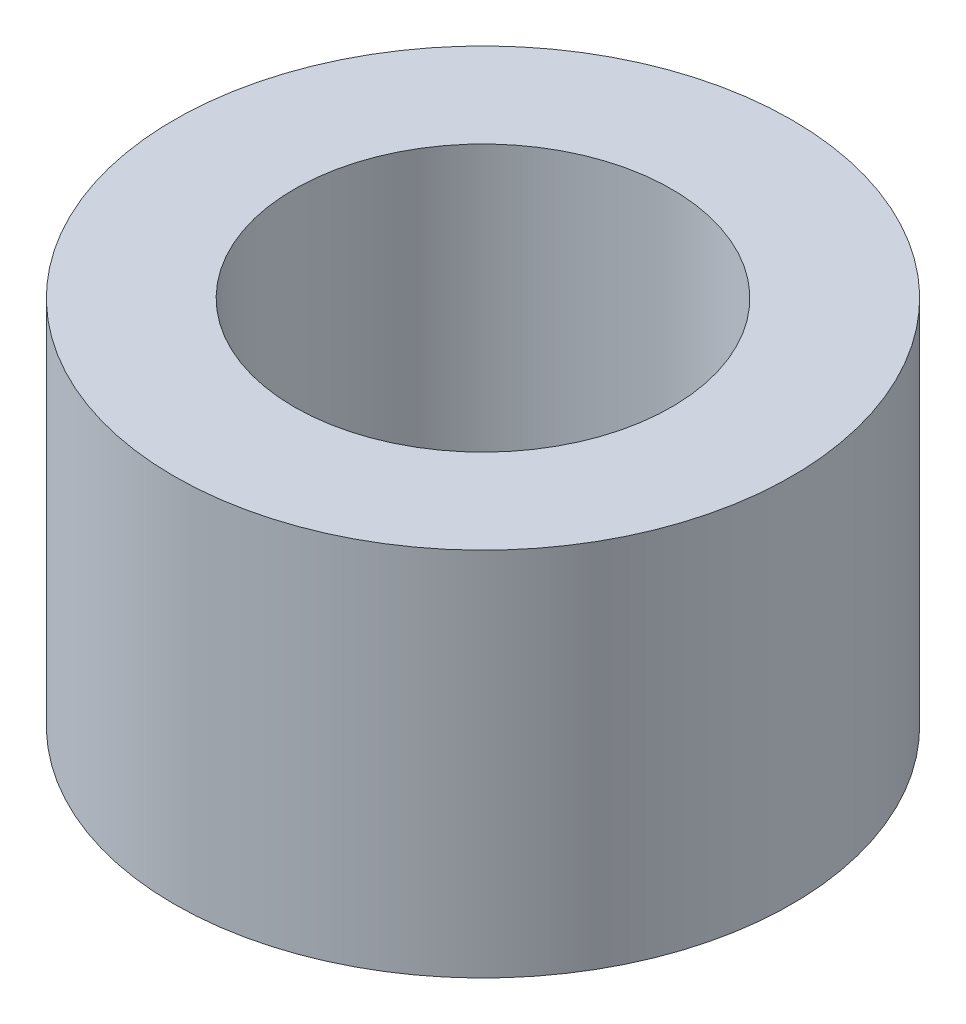
SolidWorks part; units mm, degrees
material "6061-T6 (SS)"
ref_plane "Front Plane" through (0, 0, 0) normal (0, 0, 1) x (1, 0, 0)
ref_plane "Top Plane" through (0, 0, 0) normal (0, 1, 0) x (1, 0, 0)
ref_plane "Right Plane" through (0, 0, 0) normal (1, 0, 0) x (0, 0, -1)
sketch "Sketch1" plane through (0, 0, 0) normal (0, 1, 0) x (1, 0, 0)
  circle A0 centre (0, 0) radius 7.9375
  circle A1 centre (0, 0) radius 4.8514
  dimension "D1" = 9.7028
  dimension "D2" = 15.875
extrude "Boss-Extrude1" add sketch "Sketch1" along normal blind 9.525
